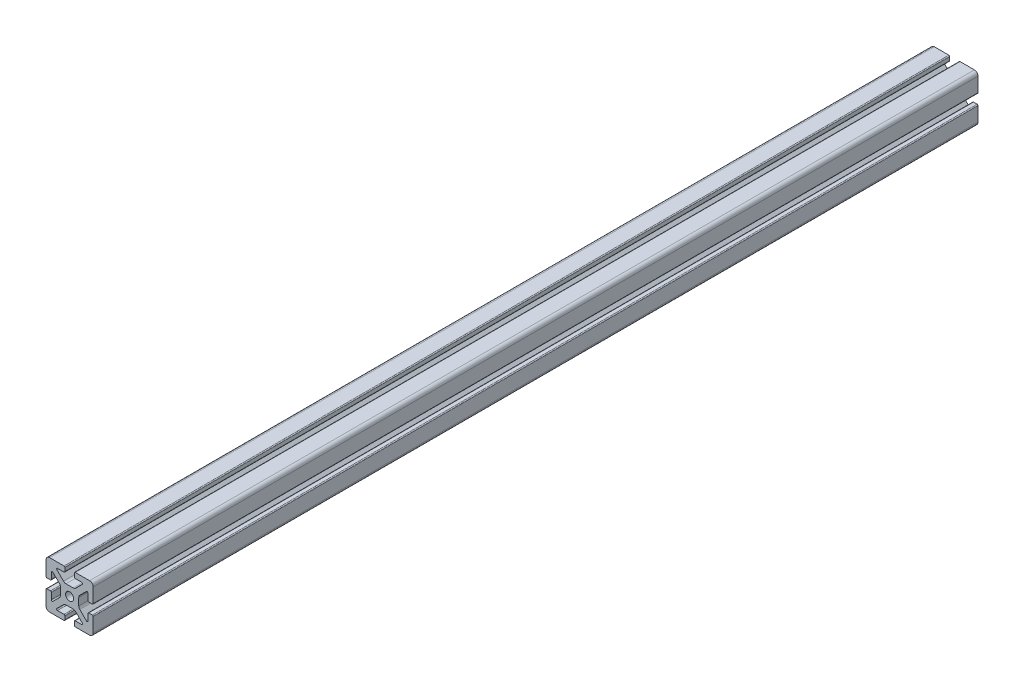
SolidWorks part; units mm, degrees
ref_plane "Front Plane" through (0, 0, 0) normal (0, 0, 1) x (1, 0, 0)
ref_plane "Top Plane" through (0, 0, 0) normal (0, 1, 0) x (1, 0, 0)
ref_plane "Right Plane" through (0, 0, 0) normal (1, 0, 0) x (0, 0, -1)
sketch "Sketch1" plane through (0, 0, 0) normal (0, 0, 1) x (1, 0, 0)
  line L2 (-20, 16.952) -> (-20, 4.7625)
  line L3 (-16.952, 20) -> (-4.7625, 20)
  line L4 (-4.0005, 19.238) -> (-4.0005, 16.2662)
  line L5 (-4.7625, 15.5042) -> (-10.2235, 15.5042)
  line L6 (-10.7623, 14.2034) -> (-5.194, 8.6351)
  line L7 (-14.2034, 10.7623) -> (-8.6351, 5.194)
  line L8 (-15.5042, 10.2235) -> (-15.5042, 4.7625)
  line L9 (-16.2662, 4.0005) -> (-19.238, 4.0005)
  line L11 (-3.0746, 7.7572) -> (3.0746, 7.7572)
  line L12 (-7.7572, 3.0746) -> (-7.7572, -3.0746)
  line L13 (16.2662, 4.0005) -> (19.238, 4.0005)
  line L14 (15.5042, 10.2235) -> (15.5042, 4.7625)
  line L15 (20, 16.952) -> (20, 4.7625)
  line L16 (16.952, 20) -> (4.7625, 20)
  line L17 (4.0005, 19.238) -> (4.0005, 16.2662)
  line L18 (4.7625, 15.5042) -> (10.2235, 15.5042)
  line L19 (7.7572, 3.0746) -> (7.7572, -3.0746)
  line L20 (10.7623, 14.2034) -> (5.194, 8.6351)
  line L21 (14.2034, 10.7623) -> (8.6351, 5.194)
  line L22 (-16.2662, -4.0005) -> (-19.238, -4.0005)
  line L23 (-15.5042, -10.2235) -> (-15.5042, -4.7625)
  line L24 (-14.2034, -10.7623) -> (-8.6351, -5.194)
  line L25 (-10.7623, -14.2034) -> (-5.194, -8.6351)
  line L26 (-4.7625, -15.5042) -> (-10.2235, -15.5042)
  line L27 (-4.0005, -19.238) -> (-4.0005, -16.2662)
  line L28 (-16.952, -20) -> (-4.7625, -20)
  line L29 (-20, -16.952) -> (-20, -4.7625)
  line L30 (20, -16.952) -> (20, -4.7625)
  line L31 (16.952, -20) -> (4.7625, -20)
  line L32 (4.0005, -19.238) -> (4.0005, -16.2662)
  line L33 (4.7625, -15.5042) -> (10.2235, -15.5042)
  line L34 (10.7623, -14.2034) -> (5.194, -8.6351)
  line L35 (14.2034, -10.7623) -> (8.6351, -5.194)
  line L36 (15.5042, -10.2235) -> (15.5042, -4.7625)
  line L37 (16.2662, -4.0005) -> (19.238, -4.0005)
  line L38 (-3.0746, -7.7572) -> (3.0746, -7.7572)
  circle A0 centre (0, 0) radius 3.4036
  arc A1 (-20, 16.952) -> (-16.952, 20) centre (-16.952, 16.952) cw
  arc A2 (-14.2034, 10.7623) -> (-15.5042, 10.2235) centre (-14.7422, 10.2235) ccw
  arc A3 (-10.2235, 15.5042) -> (-10.7623, 14.2034) centre (-10.2235, 14.7422) ccw
  arc A4 (-4.7625, 20) -> (-4.0005, 19.238) centre (-4.7625, 19.238) cw
  arc A5 (-20, 4.7625) -> (-19.238, 4.0005) centre (-19.238, 4.7625) ccw
  arc A6 (-15.5042, 4.7625) -> (-16.2662, 4.0005) centre (-16.2662, 4.7625) cw
  arc A7 (-4.0005, 16.2662) -> (-4.7625, 15.5042) centre (-4.7625, 16.2662) cw
  arc A8 (-3.0746, 7.7572) -> (-5.194, 8.6351) centre (-3.0746, 10.7544) cw
  arc A9 (-7.7572, 3.0746) -> (-8.6351, 5.194) centre (-10.7544, 3.0746) ccw
  arc A10 (15.5042, 4.7625) -> (16.2662, 4.0005) centre (16.2662, 4.7625) ccw
  arc A11 (20, 4.7625) -> (19.238, 4.0005) centre (19.238, 4.7625) cw
  arc A12 (20, 16.952) -> (16.952, 20) centre (16.952, 16.952) ccw
  arc A13 (4.7625, 20) -> (4.0005, 19.238) centre (4.7625, 19.238) ccw
  arc A14 (4.0005, 16.2662) -> (4.7625, 15.5042) centre (4.7625, 16.2662) ccw
  arc A15 (3.0746, 7.7572) -> (5.194, 8.6351) centre (3.0746, 10.7544) ccw
  arc A16 (7.7572, 3.0746) -> (8.6351, 5.194) centre (10.7544, 3.0746) cw
  arc A17 (14.2034, 10.7623) -> (15.5042, 10.2235) centre (14.7422, 10.2235) cw
  arc A18 (10.2235, 15.5042) -> (10.7623, 14.2034) centre (10.2235, 14.7422) cw
  arc A19 (-7.7572, -3.0746) -> (-8.6351, -5.194) centre (-10.7544, -3.0746) cw
  arc A20 (-3.0746, -7.7572) -> (-5.194, -8.6351) centre (-3.0746, -10.7544) ccw
  arc A21 (-4.0005, -16.2662) -> (-4.7625, -15.5042) centre (-4.7625, -16.2662) ccw
  arc A22 (-15.5042, -4.7625) -> (-16.2662, -4.0005) centre (-16.2662, -4.7625) ccw
  arc A23 (-20, -4.7625) -> (-19.238, -4.0005) centre (-19.238, -4.7625) cw
  arc A24 (-4.7625, -20) -> (-4.0005, -19.238) centre (-4.7625, -19.238) ccw
  arc A25 (-10.2235, -15.5042) -> (-10.7623, -14.2034) centre (-10.2235, -14.7422) cw
  arc A26 (-14.2034, -10.7623) -> (-15.5042, -10.2235) centre (-14.7422, -10.2235) cw
  arc A27 (-20, -16.952) -> (-16.952, -20) centre (-16.952, -16.952) ccw
  arc A28 (20, -16.952) -> (16.952, -20) centre (16.952, -16.952) cw
  arc A29 (14.2034, -10.7623) -> (15.5042, -10.2235) centre (14.7422, -10.2235) ccw
  arc A30 (10.2235, -15.5042) -> (10.7623, -14.2034) centre (10.2235, -14.7422) ccw
  arc A31 (4.7625, -20) -> (4.0005, -19.238) centre (4.7625, -19.238) cw
  arc A32 (20, -4.7625) -> (19.238, -4.0005) centre (19.238, -4.7625) ccw
  arc A33 (15.5042, -4.7625) -> (16.2662, -4.0005) centre (16.2662, -4.7625) cw
  arc A34 (4.0005, -16.2662) -> (4.7625, -15.5042) centre (4.7625, -16.2662) cw
  arc A35 (3.0746, -7.7572) -> (5.194, -8.6351) centre (3.0746, -10.7544) cw
  arc A36 (7.7572, -3.0746) -> (8.6351, -5.194) centre (10.7544, -3.0746) ccw
extrude "Boss-Extrude1" add sketch "Sketch1" along normal mid plane 750
